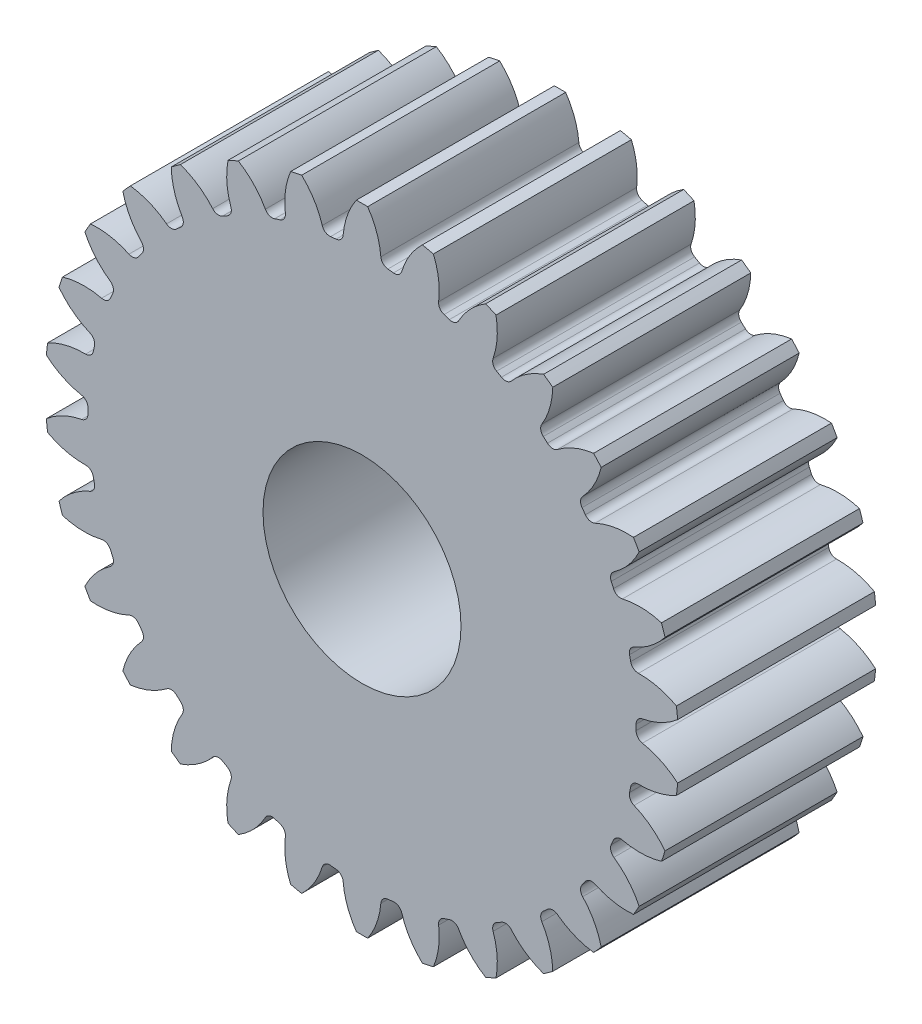
SolidWorks part; units mm, degrees
ref_plane "Front Plane" through (0, 0, 0) normal (0, 0, 1) x (1, 0, 0)
ref_plane "Top Plane" through (0, 0, 0) normal (0, 1, 0) x (1, 0, 0)
ref_plane "Right Plane" through (0, 0, 0) normal (1, 0, 0) x (0, 0, -1)
sketch "Sketch1" plane through (0, 0, 0) normal (0, 0, 1) x (1, 0, 0)
  line L0 (0, 0) -> (0, 29) construction
  line L1 (-45, 22.5) -> (45, 22.5) construction
  line L2 (-42.2862, 7.1091) -> (42.2862, 37.8909) construction
  line L3 (0, 0) -> (-15.3909, 42.2862) construction
  line L4 (-1.1781, 29) -> (1.1781, 29) construction
  line L5 (-1.1781, 29) -> (-1.1781, -7.7587) construction
  line L6 (1.1781, 29) -> (1.1781, 103.2413) construction
  circle A0 centre (0, 0) radius 22.5 construction
  circle A1 centre (0, 0) radius 24 construction
  circle A2 centre (0, 0) radius 20.7644 construction
  circle A3 centre (0, 0) radius 117.4616 construction
  circle A6 centre (-1.1781, 22.4691) radius 4.7124 construction
  circle A7 centre (3.2517, 21.0533) radius 4.7124 construction
  point P6 (0, 22.5)
  point P7 (0, 24)
  point P8 (0, 20.7644)
  point P9 (0, 0)
  point P12 (0, 22.5)
  point P15 (0, 22.5)
  point P18 (0, 0)
  point P21 (0, 29)
  point P24 (0, 0)
  point P25 (-1.1781, 22.4691)
  point P29 (-0.4288, 23.9962)
  point P30 (0, 0)
  point P31 (0, 0)
  point P32 (-1.4485, 20.7138)
  point P33 (0, 0)
  dimension "D1" = 45
  dimension "D2" = 48
  dimension "D3" = 41.5288
  dimension "D10" = 234.9232
  dimension "D12" = 9.4248
  dimension "D13" = 9.4248
  dimension "D4" = 90
  dimension "D5" = 20
  dimension "D6" = 29
  dimension "D7" = 45
  dimension "D8" = 20
  dimension "D11" = 2.3562
sketch "Sketch4" plane through (0, 0, 0) normal (0, 0, 1) x (1, 0, 0)
  line L0 (-1.1781, 22.4691) -> (1.1781, 22.5) construction
  line L1 (-45, 22.5) -> (45, 22.5) construction
  line L2 (1.1781, 29) -> (1.1781, 103.2413) construction
  line L3 (0, 22.5) -> (0, 24) construction
  line L4 (0, 0) -> (0, 29) construction
  arc A0 (-1.9596, 20.6717) -> (1.9596, 20.6717) centre (0, 0) ccw
  arc A1 (-1.4282, 21.2087) -> (-0.4288, 23.9962) centre (4.3045, 20.7262) cw
  arc A2 (1.4282, 21.2087) -> (0.4288, 23.9962) centre (-4.3045, 20.7262) ccw
  arc A3 (-0.4288, 23.9962) -> (0.4288, 23.9962) centre (0, 0) cw
  arc A4 (1.9596, 20.6717) -> (1.4282, 21.2087) centre (2.0152, 21.2581) cw
  arc A5 (-1.4282, 21.2087) -> (-1.9596, 20.6717) centre (-2.0152, 21.2581) cw
  point P21 (1.4485, 20.7138)
  point P29 (-1.4485, 20.7138)
  dimension "D1" = 0.589
extrude "Boss-Extrude1" add sketch "Sketch4" along normal blind 15
pattern_circular "CirPattern1" count 30 over 360 about axis through (0, 0, 0) along (0, 0, 1) of bodies 101
sketch "Sketch5" plane through (0, 0, 15) normal (0, 0, 1) x (1, 0, 0)
  circle A0 centre (0, 0) radius 20.7644
  dimension "D1" = 41.5288
extrude "Boss-Extrude2" add sketch "Sketch5" against normal blind 15
sketch "Sketch6" plane through (0, 0, 15) normal (0, 0, 1) x (1, 0, 0)
  circle A0 centre (0, 0) radius 7.5
  dimension "D1" = 15
extrude "Cut-Extrude1" cut sketch "Sketch6" against normal blind 20
equation "\"M\" = 1.5'Module"
equation "\"N\" = 30'Number of teeth"
equation "\"Ø\"= 20'Pressure Angle (20/24 deg)"
equation "\"CP\"= 3.14159 * \"M\"'Circular Pitch"
equation "\"Dpc\"= \"N\" * \"M\"'Diameter of Pitch Circle"
equation "\"t\"= \"CP\" / 2'Tooth Thickness"
equation "\"c\"= \"CP\" / 20'Clearence"
equation "\"r\"= \"CP\" / 8'Root Fillet Radius"
equation "\"a\"= \"M\"'Addentum"
equation "\"b\"= \"a\" + \"c\"'Deduntum"
equation "\"Da\"= \"Dpc\" + ( 2 * \"a\" )'Addentum circle Diameter"
equation "\"Db\"= \"Dpc\" - ( 2 * \"b\" )'Deduntum Circle Diameter"
equation "\"D1@Sketch1\"=\"Dpc\""
equation "\"D2@Sketch1\"=\"Da\""
equation "\"D3@Sketch1\"=\"Db\""
equation "\"D4@Sketch1\"=\"Dpc\"*2"
equation "\"D5@Sketch1\"=\"Ø\""
equation "\"D6@Sketch1\"=(\"Da\"/2)+5"
equation "\"D7@Sketch1\"=\"D4@Sketch1\"/2"
equation "\"D8@Sketch1\"=\"Ø\""
equation "\"D11@Sketch1\"=\"t\""
equation "\"D12@Sketch1\"=\"CP\"*2"
equation "\"D13@Sketch1\"= \"CP\" * 2"
equation "\"D1@Sketch4\"=\"r\""
equation "\"D1@CirPattern1\"=\"N\""
equation "\"H\" = 15'Central Hole"
equation "\"D1@Sketch6\"=\"H\""
equation "\"D1@Sketch5\"=\"Db\""
equation "\"T1\"= 15'Extrude Thickness"
equation "\"D1@Boss-Extrude1\"=\"T1\""
equation "\"D1@Boss-Extrude2\"=\"T1\""
